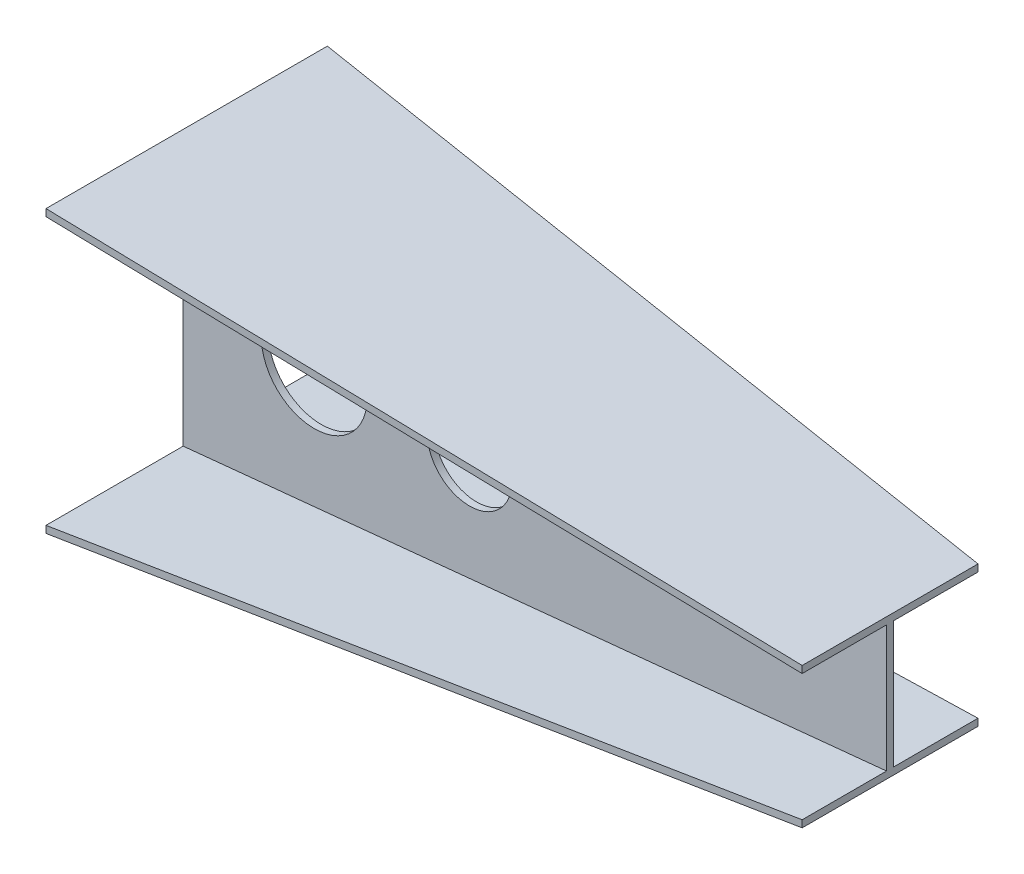
SolidWorks part; units mm, degrees
ref_plane "Front Plane" through (0, 0, 0) normal (0, 0, 1) x (1, 0, 0)
ref_plane "Top Plane" through (0, 0, 0) normal (0, 1, 0) x (1, 0, 0)
ref_plane "Right Plane" through (0, 0, 0) normal (1, 0, 0) x (0, 0, -1)
sketch "Sketch1" plane through (0, 0, 0) normal (1, 0, 0) x (0, 0, -1)
  line L1 (-205, 200) -> (195, 200)
  line L2 (-205, 200) -> (-205, 190)
  line L4 (195, 200) -> (195, 190)
  line L6 (-205, -190) -> (-205, -200)
  line L7 (-205, -200) -> (195, -200)
  line L8 (195, -190) -> (195, -200)
  line L15 (-205, -190) -> (-10, -190)
  line L16 (-5, 190) -> (-5, -790) construction
  line L18 (-205, 190) -> (-10, 190)
  line L19 (0, 0) -> (192.2403, 0) construction
  line L21 (-10, 190) -> (-10, -190)
  line L23 (0, 190) -> (0, -190)
  line L27 (0, 190) -> (195, 190)
  line L28 (0, -190) -> (195, -190)
  dimension "D1" = 400
  dimension "D2" = 10
  dimension "D3" = 400
  dimension "D4" = 10
ref_plane "Plane2" through (1000, 0, 0) normal (1, 0, 0) x (0, 0, -1)
sketch "Sketch4" plane through (1000, 0, -1000) normal (-1, 0, 0) x (0, 0, 1)
  line L1 (880, 100) -> (1130, 100)
  line L2 (880, 100) -> (880, 90)
  line L4 (1130, 100) -> (1130, 90)
  line L6 (880, -90) -> (880, -100)
  line L7 (880, -100) -> (1130, -100)
  line L8 (1130, -90) -> (1130, -100)
  line L15 (880, -90) -> (1000, -90)
  line L16 (1005, 390) -> (1005, -390) construction
  line L18 (880, 90) -> (1000, 90)
  line L19 (1010, -90) -> (1130, -90)
  line L21 (1000, 90) -> (1000, -90)
  line L23 (1010, 90) -> (1010, -90)
  line L24 (1010, 90) -> (1130, 90)
  line L26 (1010, 190) -> (1010, -190) construction
  line L27 (1000, 0) -> (820.2065, 0) construction
  dimension "D1" = 250
  dimension "D2" = 10
  dimension "D3" = 200
  dimension "D4" = 10
loft "Loft4" add profiles "Sketch1", "Sketch4"
sketch "Sketch5" plane through (0, 0, 10) normal (0, 0, 1) x (1, 0, 0)
  circle A4 centre (186.3772, 0) radius 75.2451
  circle A5 centre (407.0469, 0) radius 60.1765
extrude "Cut-Extrude1" cut sketch "Sketch5" against normal blind 10
